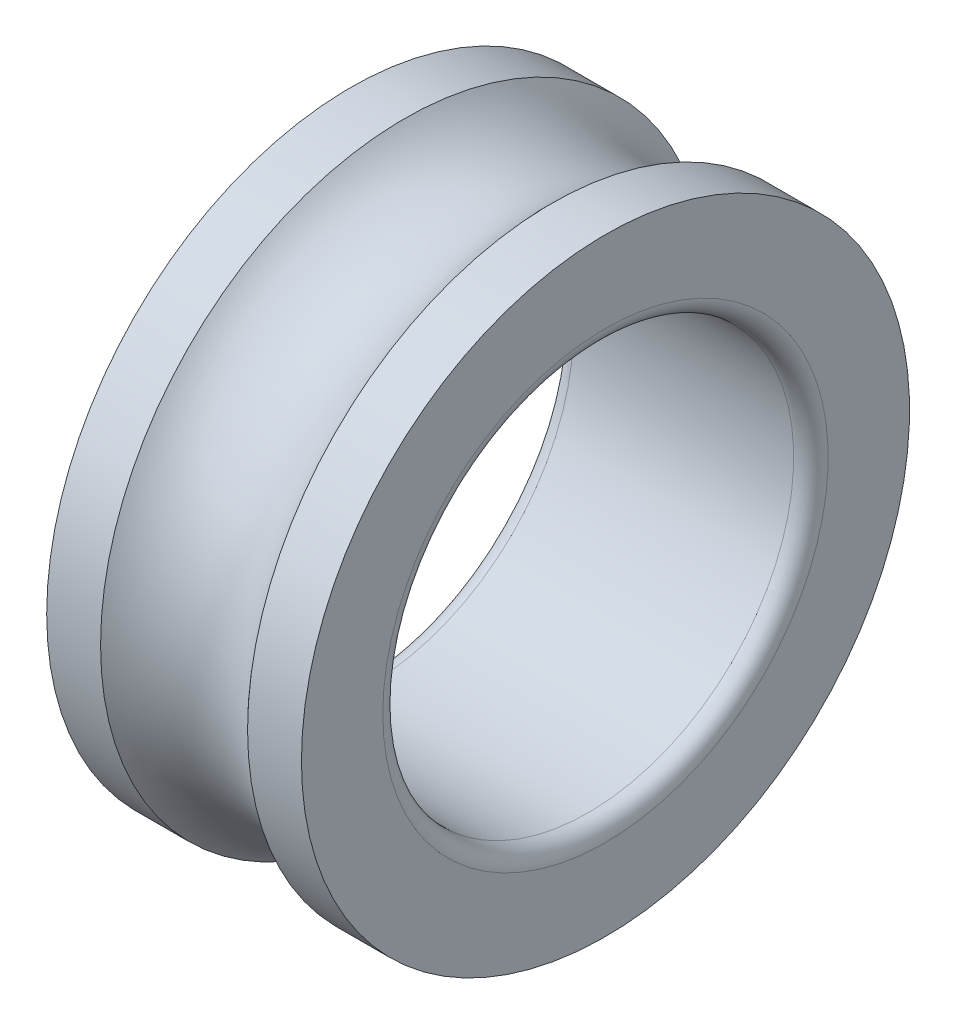
SolidWorks part; units mm, degrees
ref_plane "Front Plane" through (0, 0, 0) normal (0, 0, 1) x (1, 0, 0)
ref_plane "Top Plane" through (0, 0, 0) normal (0, 1, 0) x (1, 0, 0)
ref_plane "Right Plane" through (0, 0, 0) normal (1, 0, 0) x (0, 0, -1)
sketch "Sketch1" plane through (0, 0, 0) normal (0, 0, 1) x (1, 0, 0)
  line L0 (-12.2619, 0) -> (14.4322, 0) construction
  line L1 (0, 25) -> (0, 0) construction
  line L2 (-15.5, 37) -> (-8.9443, 37)
  line L3 (-15.5, 37) -> (-15.5, 27.1)
  line L4 (-13.4, 25) -> (13.4, 25)
  line L5 (15.5, 37) -> (15.5, 27.1)
  line L6 (-15.5, 37) -> (15.5, 25) construction
  line L7 (-15.5, 25) -> (15.5, 37) construction
  line L8 (8.9443, 37) -> (15.5, 37)
  arc A0 (-8.9443, 37) -> (8.9443, 37) centre (0, 45) ccw
  arc A1 (13.4, 25) -> (15.5, 27.1) centre (13.4, 27.1) ccw
  arc A2 (-15.5, 27.1) -> (-13.4, 25) centre (-13.4, 27.1) ccw
  point P3 (0, 31)
  dimension "D5" = 12
  dimension "D6" = 2.1
  dimension "D1" = 31
  dimension "D2" = 25
  dimension "D3" = 37
  dimension "D4" = 8
revolve "Revolve1" add sketch "Sketch1" angle 360 about L0
